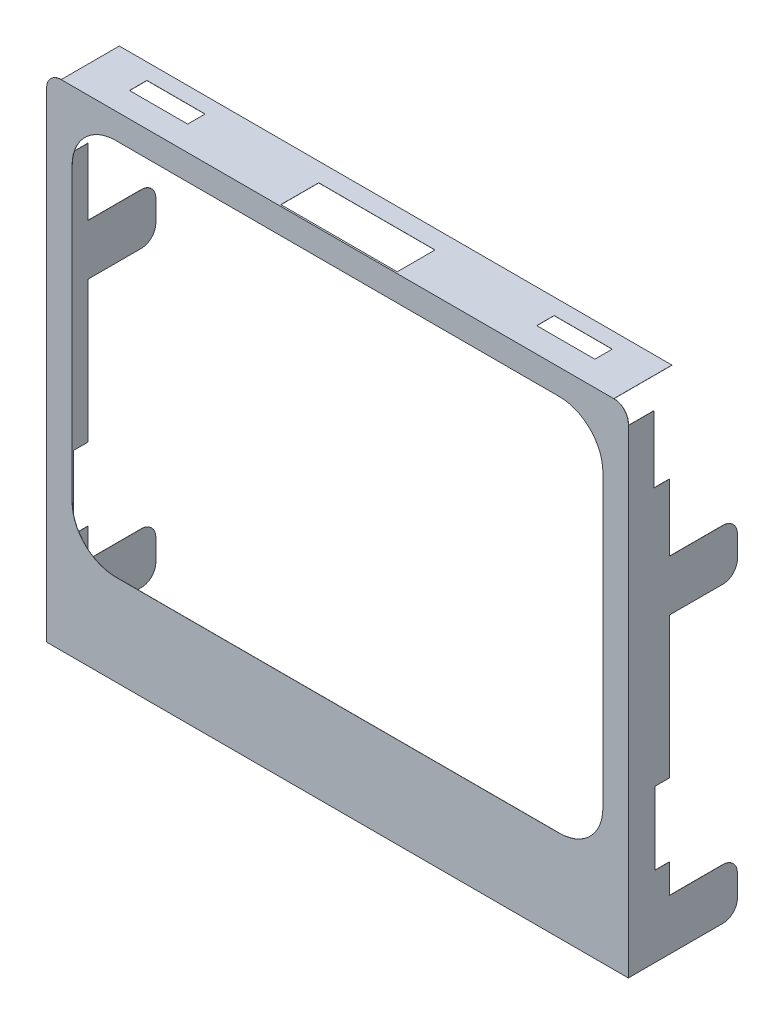
SolidWorks part; units mm, degrees
material "Liga 1060"
ref_plane "Plano frontal" through (0, 0, 0) normal (0, 0, 1) x (1, 0, 0)
ref_plane "Plano superior" through (0, 0, 0) normal (0, 1, 0) x (1, 0, 0)
ref_plane "Plano direito" through (0, 0, 0) normal (1, 0, 0) x (0, 0, -1)
sketch "Esboço1" plane through (0, 0, 0) normal (0, 0, 1) x (1, 0, 0)
  line L0 (20, 22.5264) -> (20, 43.0397) construction
  line L1 (0, 0) -> (40, 0)
  line L2 (0, 0) -> (0, 33)
  line L3 (1, 34) -> (39, 34)
  line L4 (40, 0) -> (40, 33)
  line L5 (4.75, 6.25) -> (35.25, 6.25)
  line L6 (1.75, 9.25) -> (1.75, 29.25)
  line L7 (4.75, 32.25) -> (35.25, 32.25)
  line L8 (38.25, 9.25) -> (38.25, 29.25)
  line L9 (1.75, 6.25) -> (38.25, 32.25) construction
  line L10 (1.75, 32.25) -> (38.25, 6.25) construction
  arc A0 (1.75, 9.25) -> (4.75, 6.25) centre (4.75, 9.25) ccw
  arc A1 (35.25, 6.25) -> (38.25, 9.25) centre (35.25, 9.25) ccw
  arc A2 (38.25, 29.25) -> (35.25, 32.25) centre (35.25, 29.25) ccw
  arc A3 (1.75, 29.25) -> (4.75, 32.25) centre (4.75, 29.25) cw
  arc A4 (0, 33) -> (1, 34) centre (1, 33) cw
  arc A5 (40, 33) -> (39, 34) centre (39, 33) ccw
  point P5 (20, 19.25)
  point P26 (0, 34)
  dimension "D6" = 3
  dimension "D7" = 1
  dimension "D1" = 34
  dimension "D2" = 40
  dimension "D3" = 36.5
  dimension "D4" = 1.75
  dimension "D5" = 26
extrude "Ressalto-extrusão1" add sketch "Esboço1" along normal blind 0.01
sketch "Esboço2" plane through (0, 0, 0) normal (0, -1, 0) x (1, 0, 0)
  line L0 (0, 0.01) -> (40, 0.01) construction
  line L1 (1, -3.99) -> (3, -3.99)
  line L2 (1, -3.99) -> (1, 0.01)
  line L3 (1, 0.01) -> (39, 0.01)
  line L4 (39, -3.99) -> (39, 0.01)
  line L5 (1, -3.99) -> (39, 0.01) construction
  line L6 (1, 0.01) -> (39, -3.99) construction
  line L7 (20, -1.99) -> (20, 2.3262) construction
  line L8 (0, 0.01) -> (0, 0) construction
  line L9 (40, 0.01) -> (40, 0) construction
  line L10 (12, -3.99) -> (39, -3.99)
  line L11 (17.25, -1.49) -> (22.75, -1.49)
  line L12 (17.25, -1.49) -> (17.25, -2.49)
  line L13 (17.25, -2.49) -> (22.75, -2.49)
  line L14 (22.75, -1.49) -> (22.75, -2.49)
  line L15 (17.25, -1.49) -> (22.75, -2.49) construction
  line L16 (17.25, -2.49) -> (22.75, -1.49) construction
  line L18 (3, -3.99) -> (3, -2.8321)
  line L19 (3, -2.8321) -> (12, -2.8321)
  line L20 (12, -3.99) -> (12, -2.8321)
  point P0 (20, -1.99)
  point P13 (20, -1.99)
  dimension "D1" = 38
  dimension "D2" = 4
  dimension "D3" = 1
  dimension "D4" = 5.5
  dimension "D5" = 2
  dimension "D6" = 9
extrude "Ressalto-extrusão2" add sketch "Esboço2" against normal blind 0.01
sketch "Esboço3" plane through (40, 0, 0) normal (1, 0, 0) x (0, 0, -1)
  line L0 (4.5527, 3.5) -> (2.83, 3.5)
  line L1 (-0.01, 0) -> (3.99, 0)
  line L2 (-0.01, 0) -> (-0.01, 32.9)
  line L3 (-0.01, 32.9) -> (1.7435, 32.9)
  line L4 (-0.01, 0) -> (-0.01, 33) construction
  line L5 (3.99, 0) -> (6.49, 0)
  line L7 (4.5527, 3.5) -> (6.49, 3.5)
  line L8 (7.49, 1) -> (7.49, 2.5)
  line L9 (2.83, 3.5) -> (2.83, 5.5)
  line L10 (2.83, 5.5) -> (1.83, 5.5)
  line L11 (1.83, 5.5) -> (1.83, 10.5)
  line L12 (1.83, 10.5) -> (2.83, 10.5)
  line L13 (2.83, 10.5) -> (2.83, 20.2)
  line L14 (2.83, 20.2) -> (6.49, 20.2)
  line L15 (7.49, 21.2) -> (7.49, 22.7)
  line L16 (6.49, 23.7) -> (2.83, 23.7)
  line L17 (2.83, 23.7) -> (2.83, 28.3)
  line L18 (2.83, 28.3) -> (1.7435, 28.3)
  line L19 (1.7435, 28.3) -> (1.7435, 32.9)
  arc A0 (6.49, 0) -> (7.49, 1) centre (6.49, 1) ccw
  arc A1 (7.49, 2.5) -> (6.49, 3.5) centre (6.49, 2.5) ccw
  arc A2 (6.49, 20.2) -> (7.49, 21.2) centre (6.49, 21.2) ccw
  arc A3 (7.49, 22.7) -> (6.49, 23.7) centre (6.49, 22.7) ccw
  point P23 (7.49, 0)
  point P26 (7.49, 3.5)
  point P29 (7.49, 20.2)
  point P32 (7.49, 23.7)
  dimension "D12" = 1
  dimension "D1" = 4
  dimension "D2" = 3.5
  dimension "D3" = 3.5
  dimension "D4" = 2
  dimension "D5" = 5
  dimension "D6" = 3.5
  dimension "D7" = 1.16
  dimension "D8" = 1
  dimension "D9" = 16.7
  dimension "D10" = 4.6
  dimension "D11" = 4.6
extrude "Ressalto-extrusão3" add sketch "Esboço3" against normal blind 0.01
sketch "Esboço4" plane through (0, 0, 0) normal (-1, 0, 0) x (0, 0, 1)
  line L19 (-6.49, 0) -> (0, 0)
  line L20 (0, 0) -> (0, 32.9)
  line L21 (0, 32.9) -> (-1.7435, 32.9)
  line L22 (-1.7435, 32.9) -> (-1.7435, 28.3)
  line L23 (-1.7435, 28.3) -> (-2.83, 28.3)
  line L24 (-2.83, 28.3) -> (-2.83, 23.7)
  line L25 (-2.83, 23.7) -> (-6.49, 23.7)
  line L26 (-7.49, 22.7) -> (-7.49, 21.2)
  line L27 (-6.49, 20.2) -> (-2.83, 20.2)
  line L28 (-2.83, 20.2) -> (-2.83, 10.5)
  line L29 (-2.83, 10.5) -> (-1.83, 10.5)
  line L30 (-1.83, 10.5) -> (-1.83, 5.5)
  line L31 (-1.83, 5.5) -> (-2.83, 5.5)
  line L32 (-2.83, 5.5) -> (-2.83, 3.5)
  line L33 (-2.83, 3.5) -> (-6.49, 3.5)
  line L34 (-7.49, 2.5) -> (-7.49, 1)
  line L35 (-6.49, 0) -> (0, 0)
  line L36 (0, 0) -> (0, 32.9)
  line L37 (0, 32.9) -> (-1.7435, 32.9)
  line L38 (-1.7435, 32.9) -> (-1.7435, 28.3)
  line L39 (-1.7435, 28.3) -> (-2.83, 28.3)
  line L40 (-2.83, 28.3) -> (-2.83, 23.7)
  line L41 (-2.83, 23.7) -> (-6.49, 23.7)
  line L42 (-7.49, 22.7) -> (-7.49, 21.2)
  line L43 (-6.49, 20.2) -> (-2.83, 20.2)
  line L44 (-2.83, 20.2) -> (-2.83, 10.5)
  line L45 (-2.83, 10.5) -> (-1.83, 10.5)
  line L46 (-1.83, 10.5) -> (-1.83, 5.5)
  line L47 (-1.83, 5.5) -> (-2.83, 5.5)
  line L48 (-2.83, 5.5) -> (-2.83, 3.5)
  line L49 (-2.83, 3.5) -> (-6.49, 3.5)
  line L50 (-7.49, 2.5) -> (-7.49, 1)
  arc A4 (-6.49, 23.7) -> (-7.49, 22.7) centre (-6.49, 22.7) ccw
  arc A5 (-6.49, 23.7) -> (-7.49, 22.7) centre (-6.49, 22.7) ccw
  arc A6 (-7.49, 21.2) -> (-6.49, 20.2) centre (-6.49, 21.2) ccw
  arc A7 (-7.49, 21.2) -> (-6.49, 20.2) centre (-6.49, 21.2) ccw
  arc A8 (-6.49, 3.5) -> (-7.49, 2.5) centre (-6.49, 2.5) ccw
  arc A9 (-6.49, 3.5) -> (-7.49, 2.5) centre (-6.49, 2.5) ccw
  arc A10 (-7.49, 1) -> (-6.49, 0) centre (-6.49, 1) ccw
  arc A11 (-7.49, 1) -> (-6.49, 0) centre (-6.49, 1) ccw
  dimension "D1" = 0
extrude "Ressalto-extrusão6" add sketch "Esboço4" against normal blind 0.01 separate body
sketch "Esboço5" plane through (0, 34, 0) normal (0, 1, 0) x (1, 0, 0)
  line L0 (39, 3.99) -> (39, 0) construction
  line L1 (12, 3.99) -> (39, 3.99) construction
  line L2 (1, 0) -> (1, 3.99) construction
  line L3 (39, 3.99) -> (39, -0.01)
  line L4 (1, 3.99) -> (39, 3.99)
  line L5 (1, -0.01) -> (1, 3.99)
  line L6 (39, -0.01) -> (1, -0.01) construction
  line L7 (24, 2.7) -> (16, 2.7)
  line L8 (24, 2.7) -> (24, 0.1)
  line L9 (24, 0.1) -> (16, 0.1)
  line L10 (16, 2.7) -> (16, 0.1)
  line L11 (24, 2.7) -> (16, 0.1) construction
  line L12 (24, 0.1) -> (16, 2.7) construction
  line L13 (20, 1.4) -> (20, -1.0759) construction
  line L14 (39, -0.01) -> (1, -0.01)
  line L15 (4, 1.69) -> (8, 2.89) construction
  line L16 (36, 2.89) -> (32, 2.89)
  line L17 (36, 2.89) -> (36, 1.69)
  line L18 (36, 1.69) -> (32, 1.69)
  line L19 (32, 2.89) -> (32, 1.69)
  line L20 (36, 2.89) -> (32, 1.69) construction
  line L21 (36, 1.69) -> (32, 2.89) construction
  line L22 (4, 2.89) -> (8, 1.69) construction
  line L23 (8, 2.89) -> (8, 1.69)
  line L24 (4, 1.69) -> (8, 1.69)
  line L25 (4, 2.89) -> (4, 1.69)
  line L26 (4, 2.89) -> (8, 2.89)
  line L29 (39, 0) -> (1, 0) construction
  point P5 (20, 1.4)
  point P16 (34, 2.29)
  point P25 (6, 2.29)
  dimension "D1" = 2.6
  dimension "D2" = 8
  dimension "D3" = 4
  dimension "D4" = 1.2
  dimension "D5" = 1.7
  dimension "D6" = 3
  dimension "D7" = 0.1
extrude "Ressalto-extrusão8" add sketch "Esboço5" against normal blind 0.01
combine bodies "Combinar2" operation type add bodies to combine 104 106
